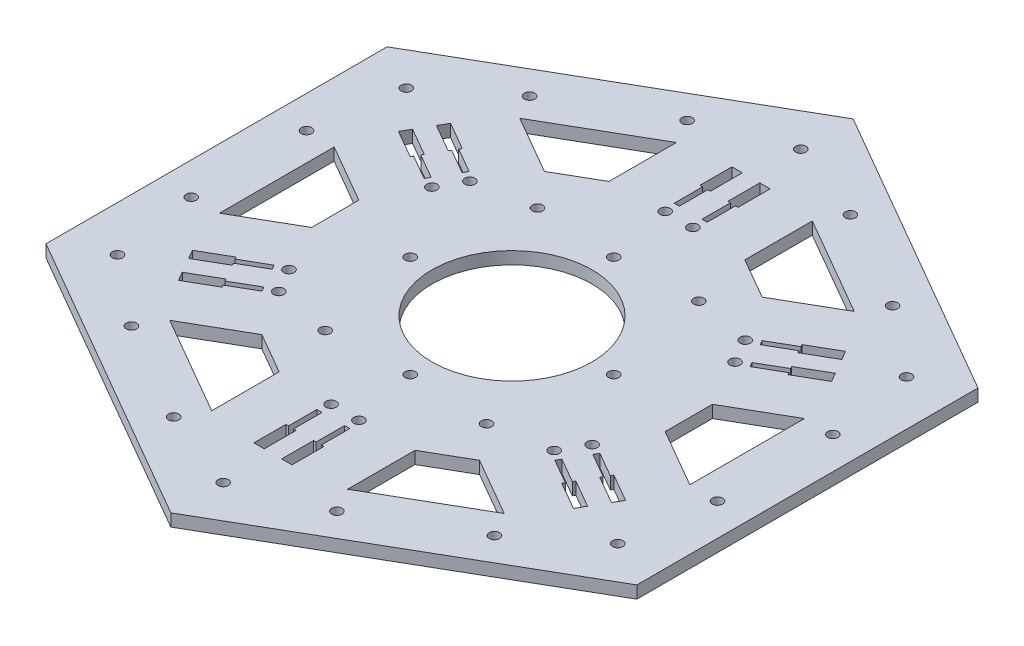
SolidWorks part; units mm, degrees
ref_plane "Front Plane" through (0, 0, 0) normal (0, 0, 1) x (1, 0, 0)
ref_plane "Top Plane" through (0, 0, 0) normal (0, 1, 0) x (1, 0, 0)
ref_plane "Right Plane" through (0, 0, 0) normal (1, 0, 0) x (0, 0, -1)
sketch "Sketch2" plane through (0, 0, 0) normal (0, 1, 0) x (1, 0, 0)
  line L1 (0, -117.3176) -> (101.6, -58.6588)
  line L2 (101.6, -58.6588) -> (101.6, 58.6588)
  line L3 (101.6, 58.6588) -> (0, 117.3176)
  line L4 (0, 117.3176) -> (-101.6, 58.6588)
  line L5 (-101.6, 58.6588) -> (-101.6, -58.6588)
  line L6 (-101.6, -58.6588) -> (0, -117.3176)
  circle A0 centre (0, 0) radius 101.6 construction
  dimension "D1" = 203.2
extrude "Boss-Extrude1" add sketch "Sketch2" along normal blind 4.25
sketch "Sketch3" plane through (0, 4.25, 0) normal (0, 1, 0) x (1, 0, 0)
  line L0 (-101.6, 0) -> (101.6, 0)
  line L1 (-101.6, 58.6588) -> (-101.6, -58.6588) construction
  line L2 (101.6, -58.6588) -> (101.6, 58.6588) construction
  line L3 (-50.8, 87.9882) -> (50.8, -87.9882)
  line L4 (0, 117.3176) -> (-101.6, 58.6588) construction
  line L5 (0, -117.3176) -> (101.6, -58.6588) construction
  line L6 (50.8, 87.9882) -> (-50.8, -87.9882)
  line L7 (101.6, 58.6588) -> (0, 117.3176) construction
  line L8 (-101.6, -58.6588) -> (0, -117.3176) construction
  line L10 (-23.365, -79.9024) -> (-23.365, -56.716)
  line L13 (-101.6, -58.6588) -> (0, 0)
  line L14 (-57.515, -60.1859) -> (-37.435, -48.5927)
  line L15 (-57.515, -60.1859) -> (-23.365, -79.9024)
  line L16 (-23.365, -56.716) -> (-37.435, -48.5927)
  line L17 (-80.88, 19.7165) -> (-60.8, 8.1234)
  line L18 (-80.88, -19.7165) -> (-80.88, 19.7165)
  line L19 (-80.88, -19.7165) -> (-60.8, -8.1234)
  line L20 (-60.8, 8.1234) -> (-60.8, -8.1234)
  line L21 (0, 0) -> (0, -117.3176)
  line L22 (-101.6, 58.6588) -> (101.6, -58.6588)
  line L23 (23.365, -79.9024) -> (23.365, -56.716)
  line L24 (57.515, -60.1859) -> (23.365, -79.9024)
  line L25 (57.515, -60.1859) -> (37.435, -48.5927)
  line L26 (23.365, -56.716) -> (37.435, -48.5927)
  line L27 (80.88, -19.7165) -> (60.8, -8.1234)
  line L28 (60.8, 8.1234) -> (60.8, -8.1234)
  line L29 (80.88, -19.7165) -> (80.88, 19.7165)
  line L30 (80.88, 19.7165) -> (60.8, 8.1234)
  line L31 (57.515, 60.1859) -> (37.435, 48.5927)
  line L32 (23.365, 79.9024) -> (57.515, 60.1859)
  line L33 (37.435, 48.5927) -> (23.365, 56.716)
  line L34 (23.365, 79.9024) -> (23.365, 56.716)
  line L35 (-23.365, 79.9024) -> (-23.365, 56.716)
  line L36 (-23.365, 79.9024) -> (-57.515, 60.1859)
  line L37 (-57.515, 60.1859) -> (-37.435, 48.5927)
  line L38 (-37.435, 48.5927) -> (-23.365, 56.716)
extrude "Cut-Extrude1" cut sketch "Sketch3" against normal blind 4.25 contours L6 L16 L14 L15 | L10 L16 L6 L15 | L26 L23 L24 L3 | L26 L3 L24 L25 | L27 L29 L0 L28 | L29 L30 L28 L0 | L33 L31 L32 L6 | L32 L34 L33 L6 | L37 L38 L3 L36 | L3 L38 L35 L36 | L17 L20 L19 L18
sketch "Sketch4" plane through (0, 4.25, 0) normal (0, 1, 0) x (1, 0, 0)
  line L0 (0, 0) -> (-101.6, 0) construction
  line L1 (-101.6, 58.6588) -> (-101.6, -58.6588) construction
  line L2 (-90.5, 0) -> (-90.5, 19.83) construction
  line L4 (-101.6, -58.6588) -> (101.6, 58.6588) construction
  line L5 (0, -117.3176) -> (0, 117.3176) construction
  line L6 (0, 0) -> (-101.6, 58.6588) construction
  point P8 (-90.5, -19.83)
  point P17 (-62.4233, 68.4603)
  point P20 (-28.0767, 88.2903)
  point P22 (-62.4233, -68.4603)
  point P23 (-28.0767, -88.2903)
  point P25 (28.0767, -88.2903)
  point P26 (62.4233, -68.4603)
  point P27 (90.5, -19.83)
  point P28 (90.5, 19.83)
  point P29 (62.4233, 68.4603)
  point P30 (28.0767, 88.2903)
  dimension "D1" = 11.1
hole_wizard "#37 (0.14015748) Diameter Hole1" positions "Sketch5" profile "Sketch6" hole size "#37" standard "ANSI Inch" end condition through all
sketch "Sketch5" plane through (0, 4.25, 0) normal (0, 1, 0) x (1, 0, 0)
  point P0 (62.4233, 68.4603)
  point P3 (90.5, 19.83)
  point P6 (90.5, -19.83)
  point P9 (62.4233, -68.4603)
  point P12 (28.0767, -88.2903)
  point P15 (-28.0767, -88.2903)
  point P18 (-62.4233, -68.4603)
  point P21 (-90.5, -19.83)
  point P24 (-90.5, 19.83)
  point P27 (-62.4233, 68.4603)
  point P30 (-28.0767, 88.2903)
  point P33 (28.0767, 88.2903)
sketch "Sketch6" plane through (62.4233, 4.25, -68.4603) normal (1, 0, 0) x (0, 0, 1)
  line L0 (0, 0) -> (0, 4.25)
  line L1 (0, 4.25) -> (1.78, 4.25)
  line L2 (1.78, 4.25) -> (1.78, 0)
  line L5 (1.78, 0) -> (0, 0)
  line L11 (0, -6.35) -> (0, 107.95) construction
  dimension "Thru Hole Dia." = 3.56
  dimension "Thru Hole Depth" = 4.25
sketch "Sketch7" plane through (0, 4.25, 0) normal (0, 1, 0) x (1, 0, 0)
  line L4 (-101.6, 58.6588) -> (101.6, -58.6588) construction
  line L5 (101.6, 58.6588) -> (-101.6, -58.6588) construction
  line L6 (0, -117.3176) -> (0, 117.3176) construction
  line L8 (101.6, -58.6588) -> (101.6, 58.6588) construction
  line L9 (0, -117.3176) -> (101.6, -58.6588) construction
  point P0 (86.0115, 49.6588)
  point P1 (86.0115, -49.6588)
  point P2 (0, 99.3176)
  point P3 (-86.0115, -49.6588)
  point P4 (-86.0115, 49.6588)
  point P5 (0, -99.3176)
  dimension "D1" = 18
  dimension "D2" = 18
  dimension "D3" = 18
  dimension "D4" = 15.5885
  dimension "D5" = 15.5885
  dimension "D6" = 18
  dimension "D7" = 18
  dimension "D8" = 18
hole_wizard "#37 (0.14015748) Diameter Hole2" positions "3DSketch1" profile "Sketch8" hole size "#37" standard "ANSI Inch" end condition through all
sketch3d "3DSketch1"
  point P0 (86.0115, 4.25, -49.6588)
  point P3 (86.0115, 4.25, 49.6588)
  point P6 (0, 4.25, 99.3176)
  point P9 (-86.0115, 4.25, 49.6588)
  point P12 (-86.0115, 4.25, -49.6588)
  point P15 (0, 4.25, -99.3176)
sketch "Sketch8" plane through (86.0115, 4.25, -49.6588) normal (1, 0, 0) x (0, 0, 1)
  line L0 (0, 0) -> (0, 4.25)
  line L1 (0, 4.25) -> (1.78, 4.25)
  line L2 (1.78, 4.25) -> (1.78, 0)
  line L5 (1.78, 0) -> (0, 0)
  line L11 (0, -6.35) -> (0, 107.95) construction
  dimension "Thru Hole Dia." = 3.56
  dimension "Thru Hole Depth" = 4.25
sketch "Sketch9" plane through (0, 4.25, 0) normal (0, 1, 0) x (1, 0, 0)
  line L0 (-101.6, 0) -> (101.6, 0) construction
  line L1 (-101.6, 58.6588) -> (-101.6, -58.6588) construction
  line L2 (101.6, -58.6588) -> (101.6, 58.6588) construction
  line L3 (0, 117.3176) -> (0, -117.3176) construction
  point P10 (15, 15)
  point P11 (15, -15)
  point P12 (-15, -15)
  point P13 (-15, 15)
  point P14 (27.75, 36.5)
  point P15 (27.75, -36.5)
  point P16 (-27.75, -36.5)
  point P17 (-27.75, 36.5)
  dimension "D1" = 30
  dimension "D2" = 15
  dimension "D3" = 30
  dimension "D4" = 15
  dimension "D5" = 30
  dimension "D6" = 30
  dimension "D7" = 15
  dimension "D8" = 15
  dimension "D9" = 73
  dimension "D10" = 55.5
  dimension "D11" = 73
  dimension "D12" = 36.5
  dimension "D13" = 36.5
  dimension "D14" = 27.75
hole_wizard "#37 (0.14015748) Diameter Hole3" positions "3DSketch2" profile "Sketch10" hole size "#37" standard "ANSI Inch" end condition through all
sketch3d "3DSketch2"
  point P0 (27.75, 4.25, -36.5)
  point P3 (-27.75, 4.25, -36.5)
  point P6 (-15, 4.25, -15)
  point P9 (15, 4.25, -15)
  point P12 (15, 4.25, 15)
  point P15 (-15, 4.25, 15)
  point P18 (-27.75, 4.25, 36.5)
  point P21 (27.75, 4.25, 36.5)
sketch "Sketch10" plane through (27.75, 4.25, -36.5) normal (1, 0, 0) x (0, 0, 1)
  line L0 (0, 0) -> (0, 4.25)
  line L1 (0, 4.25) -> (1.78, 4.25)
  line L2 (1.78, 4.25) -> (1.78, 0)
  line L5 (1.78, 0) -> (0, 0)
  line L11 (0, -6.35) -> (0, 107.95) construction
  dimension "Thru Hole Dia." = 3.56
  dimension "Thru Hole Depth" = 4.25
sketch "Sketch11" plane through (0, 4.25, 0) normal (0, 1, 0) x (1, 0, 0)
  line L0 (-69.6927, 43.7012) -> (-60.1665, 38.2012)
  line L2 (-60.1665, 38.2012) -> (-59.7217, 38.9716)
  line L77 (-58.8317, 40.5132) -> (-58.3867, 41.2839)
  line L78 (-58.3867, 41.2839) -> (-67.9129, 46.7839)
  line L79 (-68.008, 46.6192) -> (-69.788, 43.5362)
  line L80 (-59.7217, 38.9716) -> (-51.2532, 34.0823)
  line L81 (-58.8317, 40.5132) -> (-50.3632, 35.6239)
  line L82 (-74.477, 35.4245) -> (-64.9507, 29.9245)
  line L83 (-64.9507, 29.9245) -> (-64.5059, 30.6949)
  line L84 (-63.6157, 32.2368) -> (-63.1707, 33.0075)
  line L85 (-63.1707, 33.0075) -> (-72.697, 38.5075)
  line L86 (-72.793, 38.3413) -> (-74.573, 35.2582)
  line L87 (-64.5059, 30.6949) -> (-56.0374, 25.8056)
  line L88 (-63.6157, 32.2368) -> (-55.1472, 27.3475)
  line L89 (-50.3632, 35.6239) -> (-51.2532, 34.0823)
  line L90 (-55.1472, 27.3475) -> (-56.0374, 25.8056)
  circle A9 centre (-47.344, 32.8531) radius 1.78
  circle A10 centre (-52.1283, 24.5764) radius 1.78
  dimension "D9" = 11
  dimension "D10" = 11
  dimension "D13" = 3.56
  dimension "D14" = 3.56
  dimension "D5" = 0.89
  dimension "D7" = 0.8896
  dimension "D11" = 11
  dimension "D12" = 11
  dimension "D45" = 0.89
  dimension "D46" = 4
  dimension "D88" = 3.9091
  dimension "D89" = 4.0978
sketch "Sketch13" plane through (0, 4.25, 0) normal (0, 1, 0) x (1, 0, 0)
  line L0 (-50.3632, 35.6239) -> (-51.2532, 34.0823)
  line L1 (-51.2532, 34.0823) -> (-59.7217, 38.9716)
  line L2 (-59.7217, 38.9716) -> (-60.1665, 38.2012)
  line L5 (-67.9129, 46.7839) -> (-58.3867, 41.2839)
  line L6 (-58.3867, 41.2839) -> (-58.8317, 40.5132)
  line L7 (-58.8317, 40.5132) -> (-50.3632, 35.6239)
  line L8 (-55.1472, 27.3475) -> (-56.0374, 25.8056)
  line L9 (-56.0374, 25.8056) -> (-64.5059, 30.6949)
  line L10 (-64.5059, 30.6949) -> (-64.9507, 29.9245)
  line L11 (-64.9507, 29.9245) -> (-74.477, 35.4245)
  line L12 (-74.477, 35.4245) -> (-72.697, 38.5075)
  line L13 (-72.697, 38.5075) -> (-63.1707, 33.0075)
  line L14 (-63.1707, 33.0075) -> (-63.6157, 32.2368)
  line L15 (-63.6157, 32.2368) -> (-55.1472, 27.3475)
  line L16 (-60.1665, 38.2012) -> (-69.6927, 43.7012)
  line L17 (-69.6927, 43.7012) -> (-67.9129, 46.7839)
  line L18 (5.6696, 61.4277) -> (3.8896, 61.4277)
  line L19 (3.8896, 61.4277) -> (3.8896, 71.2063)
  line L20 (3.8896, 71.2063) -> (3, 71.2063)
  line L21 (6.5596, 82.2063) -> (6.5596, 71.2063)
  line L22 (6.5596, 71.2063) -> (5.6696, 71.2063)
  line L23 (5.6696, 71.2063) -> (5.6696, 61.4277)
  line L24 (-3.89, 61.4326) -> (-5.6704, 61.4326)
  line L25 (-5.6704, 61.4326) -> (-5.6704, 71.2112)
  line L26 (-5.6704, 71.2112) -> (-6.56, 71.2112)
  line L27 (-6.56, 71.2112) -> (-6.56, 82.2112)
  line L28 (-6.56, 82.2112) -> (-3, 82.2112)
  line L29 (-3, 82.2112) -> (-3, 71.2112)
  line L30 (-3, 71.2112) -> (-3.89, 71.2112)
  line L31 (-3.89, 71.2112) -> (-3.89, 61.4326)
  line L32 (3, 71.2063) -> (3, 82.2063)
  line L33 (3, 82.2063) -> (6.5596, 82.2063)
  line L34 (56.0327, 25.8038) -> (55.1428, 27.3454)
  line L35 (55.1428, 27.3454) -> (63.6113, 32.2347)
  line L36 (63.6113, 32.2347) -> (63.1665, 33.0051)
  line L37 (74.4725, 35.4224) -> (64.9463, 29.9224)
  line L38 (64.9463, 29.9224) -> (64.5013, 30.6931)
  line L39 (64.5013, 30.6931) -> (56.0327, 25.8038)
  line L40 (51.2572, 34.0851) -> (50.367, 35.627)
  line L41 (50.367, 35.627) -> (58.8355, 40.5163)
  line L42 (58.8355, 40.5163) -> (58.3907, 41.2867)
  line L43 (58.3907, 41.2867) -> (67.917, 46.7867)
  line L44 (67.917, 46.7867) -> (69.697, 43.7037)
  line L45 (69.697, 43.7037) -> (60.1707, 38.2037)
  line L46 (60.1707, 38.2037) -> (59.7257, 38.9744)
  line L47 (59.7257, 38.9744) -> (51.2572, 34.0851)
  line L48 (63.1665, 33.0051) -> (72.6927, 38.5051)
  line L49 (72.6927, 38.5051) -> (74.4725, 35.4224)
  line L50 (50.3632, -35.6239) -> (51.2532, -34.0823)
  line L51 (51.2532, -34.0823) -> (59.7217, -38.9716)
  line L52 (59.7217, -38.9716) -> (60.1665, -38.2012)
  line L53 (67.9129, -46.7839) -> (58.3867, -41.2839)
  line L54 (58.3867, -41.2839) -> (58.8317, -40.5132)
  line L55 (58.8317, -40.5132) -> (50.3632, -35.6239)
  line L56 (55.1472, -27.3475) -> (56.0374, -25.8056)
  line L57 (56.0374, -25.8056) -> (64.5059, -30.6949)
  line L58 (64.5059, -30.6949) -> (64.9507, -29.9245)
  line L59 (64.9507, -29.9245) -> (74.477, -35.4245)
  line L60 (74.477, -35.4245) -> (72.697, -38.5075)
  line L61 (72.697, -38.5075) -> (63.1707, -33.0075)
  line L62 (63.1707, -33.0075) -> (63.6157, -32.2368)
  line L63 (63.6157, -32.2368) -> (55.1472, -27.3475)
  line L64 (60.1665, -38.2012) -> (69.6927, -43.7012)
  line L65 (69.6927, -43.7012) -> (67.9129, -46.7839)
  line L66 (-5.6696, -61.4277) -> (-3.8896, -61.4277)
  line L67 (-3.8896, -61.4277) -> (-3.8896, -71.2063)
  line L68 (-3.8896, -71.2063) -> (-3, -71.2063)
  line L69 (-6.5596, -82.2063) -> (-6.5596, -71.2063)
  line L70 (-6.5596, -71.2063) -> (-5.6696, -71.2063)
  line L71 (-5.6696, -71.2063) -> (-5.6696, -61.4277)
  line L72 (3.89, -61.4326) -> (5.6704, -61.4326)
  line L73 (5.6704, -61.4326) -> (5.6704, -71.2112)
  line L74 (5.6704, -71.2112) -> (6.56, -71.2112)
  line L75 (6.56, -71.2112) -> (6.56, -82.2112)
  line L76 (6.56, -82.2112) -> (3, -82.2112)
  line L77 (3, -82.2112) -> (3, -71.2112)
  line L78 (3, -71.2112) -> (3.89, -71.2112)
  line L79 (3.89, -71.2112) -> (3.89, -61.4326)
  line L80 (-3, -71.2063) -> (-3, -82.2063)
  line L81 (-3, -82.2063) -> (-6.5596, -82.2063)
  line L82 (-56.0327, -25.8038) -> (-55.1428, -27.3454)
  line L83 (-55.1428, -27.3454) -> (-63.6113, -32.2347)
  line L84 (-63.6113, -32.2347) -> (-63.1665, -33.0051)
  line L85 (-74.4725, -35.4224) -> (-64.9463, -29.9224)
  line L86 (-64.9463, -29.9224) -> (-64.5013, -30.6931)
  line L87 (-64.5013, -30.6931) -> (-56.0327, -25.8038)
  line L88 (-51.2572, -34.0851) -> (-50.367, -35.627)
  line L89 (-50.367, -35.627) -> (-58.8355, -40.5163)
  line L90 (-58.8355, -40.5163) -> (-58.3907, -41.2867)
  line L91 (-58.3907, -41.2867) -> (-67.917, -46.7867)
  line L92 (-67.917, -46.7867) -> (-69.697, -43.7037)
  line L93 (-69.697, -43.7037) -> (-60.1707, -38.2037)
  line L94 (-60.1707, -38.2037) -> (-59.7257, -38.9744)
  line L95 (-59.7257, -38.9744) -> (-51.2572, -34.0851)
  line L96 (-63.1665, -33.0051) -> (-72.6927, -38.5051)
  line L97 (-72.6927, -38.5051) -> (-74.4725, -35.4224)
  circle A0 centre (-47.344, 32.8531) radius 1.78
  circle A1 centre (-52.1283, 24.5764) radius 1.78
  circle A2 centre (4.7796, 57.4277) radius 1.78
  circle A3 centre (-4.7804, 57.4326) radius 1.78
  circle A4 centre (52.1237, 24.5746) radius 1.78
  circle A5 centre (47.3479, 32.8562) radius 1.78
  circle A6 centre (47.344, -32.8531) radius 1.78
  circle A7 centre (52.1283, -24.5764) radius 1.78
  circle A8 centre (-4.7796, -57.4277) radius 1.78
  circle A9 centre (4.7804, -57.4326) radius 1.78
  circle A10 centre (-52.1237, -24.5746) radius 1.78
  circle A11 centre (-47.3479, -32.8562) radius 1.78
  dimension "D1" = 6
extrude "Cut-Extrude7" cut sketch "Sketch13" against normal blind 10
sketch "Sketch14" plane through (0, 4.25, 0) normal (0, 1, 0) x (1, 0, 0)
  point P7 (35, 0)
  point P8 (0, 35)
  point P9 (0, -35)
  point P10 (-35, 0)
  point P12 (35, 0)
  point P13 (0, -35)
  point P14 (-35, 0)
  point P15 (35, 0)
  point P16 (0, -35)
  point P17 (-35, 0)
  dimension "D1" = 35
  dimension "D2" = 4
  dimension "D3" = 4
  dimension "D4" = 4
hole_wizard "#37 (0.14015748) Diameter Hole5" positions "3DSketch5" profile "Sketch17" hole size "#37" standard "ANSI Inch" end condition through all
sketch3d "3DSketch5"
  point P0 (0, 4.25, -35)
  point P3 (35, 4.25, 0)
  point P6 (0, 4.25, 35)
  point P9 (-35, 4.25, 0)
sketch "Sketch17" plane through (0, 4.25, -35) normal (1, 0, 0) x (0, 0, 1)
  line L0 (0, 0) -> (0, 4.25)
  line L1 (0, 4.25) -> (1.78, 4.25)
  line L2 (1.78, 4.25) -> (1.78, 0)
  line L5 (1.78, 0) -> (0, 0)
  line L11 (0, -6.35) -> (0, 107.95) construction
  dimension "Thru Hole Dia." = 3.56
  dimension "Thru Hole Depth" = 4.25
sketch "Sketch18" plane through (0, 4.25, 0) normal (0, 1, 0) x (1, 0, 0)
  circle A0 centre (0, 0) radius 27.5
  dimension "D1" = 55
extrude "Cut-Extrude8" cut sketch "Sketch18" against normal blind 10
